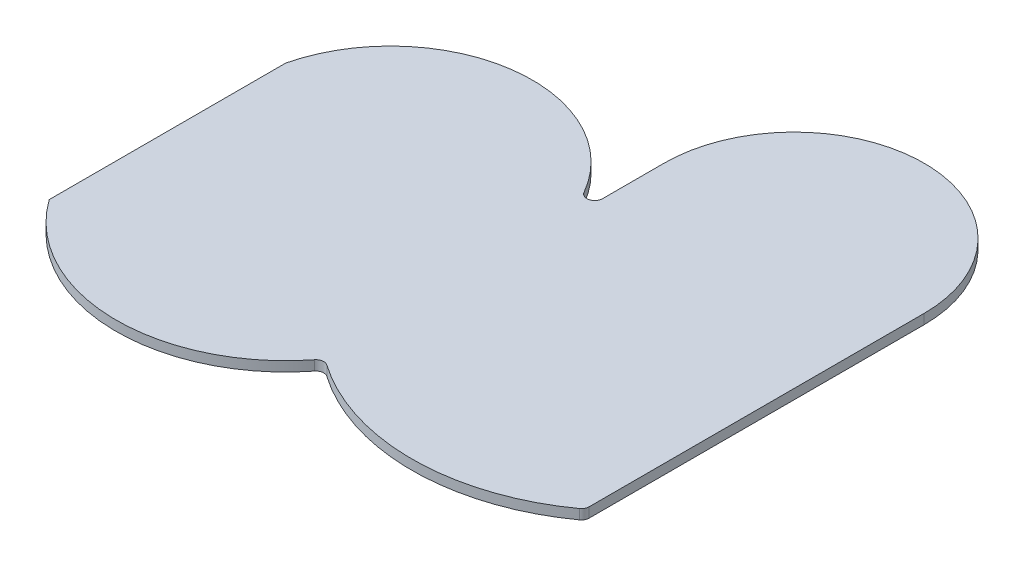
SolidWorks part; units mm, degrees
ref_plane "Front Plane" through (0, 0, 0) normal (0, 0, 1) x (1, 0, 0)
ref_plane "Top Plane" through (0, 0, 0) normal (0, 1, 0) x (1, 0, 0)
ref_plane "Right Plane" through (0, 0, 0) normal (1, 0, 0) x (0, 0, -1)
sketch "Sketch2" plane through (0, 0, 0) normal (0, 1, 0) x (1, 0, 0)
  line L0 (-1238.3387, -240) -> (48761.6613, -240) construction
  line L1 (-515, 150) -> (-165, 150) construction
  line L2 (-515, 150) -> (-515, -150)
  line L3 (-515, -150) -> (-165, -150) construction
  line L4 (-165, 150) -> (-165, -150) construction
  line L5 (-515, 150) -> (-165, -150) construction
  line L6 (-515, -150) -> (-165, 150) construction
  line L7 (-165, 150) -> (-165, 280)
  line L8 (165, 150) -> (-165, 150) construction
  line L9 (165, 150) -> (165, -150)
  line L10 (165, -150) -> (-165, -150) construction
  line L11 (-165, 150) -> (-165, -150) construction
  line L12 (165, 150) -> (-165, -150) construction
  line L13 (165, -150) -> (-165, 150) construction
  line L14 (165, 150) -> (165, 280)
  arc A0 (-515, 150) -> (-165, 150) centre (-340, 107.8693) cw
  arc A1 (-515, -150) -> (-165, -150) centre (-340, -24.8611) ccw
  arc A3 (-165, -150) -> (165, -150) centre (0, 70) ccw
  arc A4 (-165, 280) -> (165, 280) centre (0, 280) cw
  point P0 (-340, 0)
  point P9 (0, 0)
  point P11 (-340, -240)
  point P18 (0, 0)
  dimension "D3" = 180
  dimension "D4" = 90
  dimension "D6" = 275
  dimension "D7" = 165
  dimension "D8" = 430
  dimension "D1" = 300
  dimension "D2" = 350
  dimension "D5" = 330
extrude "Boss-Extrude1" add sketch "Sketch2" along normal mid plane 12.5
fillet "Fillet1" radius 10 3 edges at (165, 0, 150) (-165, 0, 150) (-165, 0, -150)
